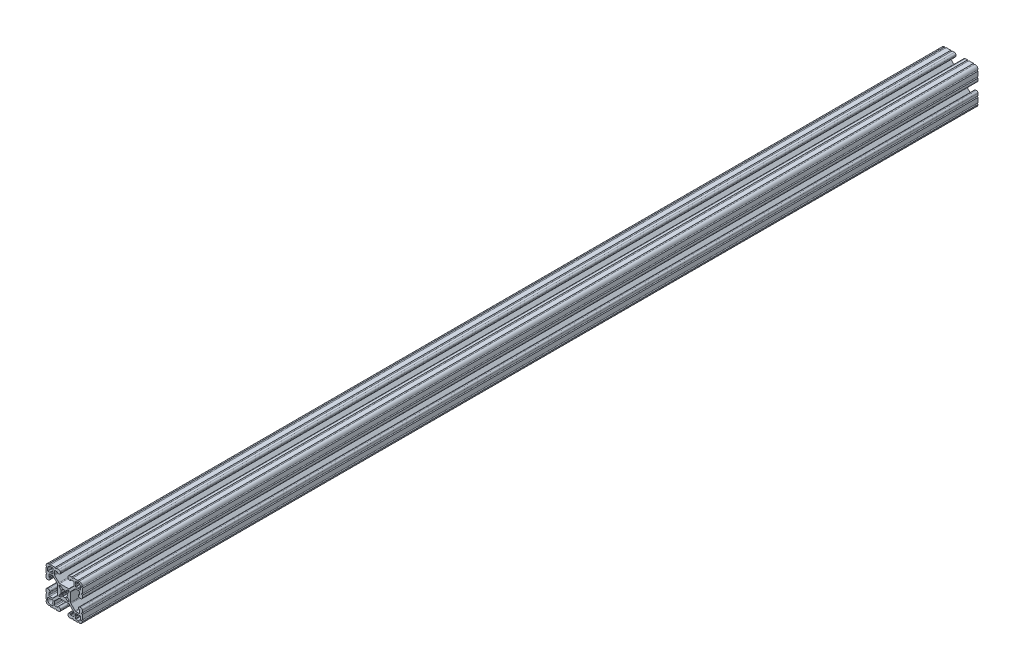
SolidWorks part; units mm, degrees
ref_plane "Front Plane" through (0, 0, 0) normal (0, 0, 1) x (1, 0, 0)
ref_plane "Top Plane" through (0, 0, 0) normal (0, 1, 0) x (1, 0, 0)
ref_plane "Right Plane" through (0, 0, 0) normal (1, 0, 0) x (0, 0, -1)
ref_plane "Plane1" through (0, 0, -2322.576) normal (0, 0, -1) x (-1, 0, 0)
sketch "Sketch1" plane through (0, 0, -2322.576) normal (0, 0, -1) x (-1, 0, 0)
  line L0 (17.2466, 14.4526) -> (17.2466, 12.2428)
  line L1 (16.8656, 11.8618) -> (15.0927, 11.8618)
  line L2 (15.0927, 11.8618) -> (14.5542, 12.4003)
  line L3 (14.5542, 12.4003) -> (14.0157, 11.8618)
  line L4 (14.0157, 11.8618) -> (12.2428, 11.8618)
  line L5 (11.8618, 12.2428) -> (11.8618, 14.0157)
  line L6 (11.8618, 14.0157) -> (12.4003, 14.5542)
  line L7 (12.4003, 14.5542) -> (11.8618, 15.0927)
  line L8 (11.8618, 15.0927) -> (11.8618, 16.8656)
  line L9 (12.2428, 17.2466) -> (14.4526, 17.2466)
  line L10 (17.2466, -12.2428) -> (17.2466, -14.4526)
  line L11 (14.4526, -17.2466) -> (12.2428, -17.2466)
  line L12 (11.8618, -16.8656) -> (11.8618, -15.0927)
  line L13 (11.8618, -15.0927) -> (12.4003, -14.5542)
  line L14 (12.4003, -14.5542) -> (11.8618, -14.0157)
  line L15 (11.8618, -14.0157) -> (11.8618, -12.2428)
  line L16 (12.2428, -11.8618) -> (14.0157, -11.8618)
  line L17 (14.0157, -11.8618) -> (14.5542, -12.4003)
  line L18 (14.5542, -12.4003) -> (15.0927, -11.8618)
  line L19 (15.0927, -11.8618) -> (16.8656, -11.8618)
  line L20 (5.1689, -3.9207) -> (5.1689, -4.9149)
  line L21 (4.9149, -5.1689) -> (3.9207, -5.1689)
  line L22 (3.2921, -4.9085) -> (1.5823, -3.1988)
  line L23 (-1.5823, -3.1988) -> (-3.2921, -4.9085)
  line L24 (-3.9207, -5.1689) -> (-4.9149, -5.1689)
  line L25 (-5.1689, -4.9149) -> (-5.1689, -3.9207)
  line L26 (-4.9085, -3.2921) -> (-3.1988, -1.5823)
  line L27 (-3.1988, 1.5823) -> (-4.9085, 3.2921)
  line L28 (-5.1689, 3.9207) -> (-5.1689, 4.9149)
  line L29 (-4.9149, 5.1689) -> (-3.9207, 5.1689)
  line L30 (-3.2921, 4.9085) -> (-1.5823, 3.1988)
  line L31 (1.5823, 3.1988) -> (3.2921, 4.9085)
  line L32 (3.9207, 5.1689) -> (4.9149, 5.1689)
  line L33 (5.1689, 4.9149) -> (5.1689, 3.9207)
  line L34 (4.9085, 3.2921) -> (3.1988, 1.5823)
  line L35 (3.1988, -1.5823) -> (4.9085, -3.2921)
  line L36 (-11.8618, -12.2428) -> (-11.8618, -14.0157)
  line L37 (-11.8618, -14.0157) -> (-12.4003, -14.5542)
  line L38 (-12.4003, -14.5542) -> (-11.8618, -15.0927)
  line L39 (-11.8618, -15.0927) -> (-11.8618, -16.8656)
  line L40 (-12.2428, -17.2466) -> (-14.4526, -17.2466)
  line L41 (-17.2466, -14.4526) -> (-17.2466, -12.2428)
  line L42 (-16.8656, -11.8618) -> (-15.0927, -11.8618)
  line L43 (-15.0927, -11.8618) -> (-14.5542, -12.4003)
  line L44 (-14.5542, -12.4003) -> (-14.0157, -11.8618)
  line L45 (-14.0157, -11.8618) -> (-12.2428, -11.8618)
  line L46 (-11.8618, 16.8656) -> (-11.8618, 15.0927)
  line L47 (-11.8618, 15.0927) -> (-12.4003, 14.5542)
  line L48 (-12.4003, 14.5542) -> (-11.8618, 14.0157)
  line L49 (-11.8618, 14.0157) -> (-11.8618, 12.2428)
  line L50 (-12.2428, 11.8618) -> (-14.0157, 11.8618)
  line L51 (-14.0157, 11.8618) -> (-14.5542, 12.4003)
  line L52 (-14.5542, 12.4003) -> (-15.0927, 11.8618)
  line L53 (-15.0927, 11.8618) -> (-16.8656, 11.8618)
  line L54 (-17.2466, 12.2428) -> (-17.2466, 14.4526)
  line L55 (-14.4526, 17.2466) -> (-12.2428, 17.2466)
  line L56 (19.05, -14.3256) -> (19.05, -9.4996)
  line L57 (19.05, -7.9756) -> (19.05, -5.6388)
  line L58 (17.4752, -4.064) -> (16.5608, -4.064)
  line L59 (14.986, -5.6388) -> (14.986, -6.35)
  line L60 (15.367, -6.731) -> (15.6972, -6.731)
  line L61 (16.0782, -7.112) -> (16.0782, -9.398)
  line L62 (15.1892, -10.287) -> (12.3756, -10.287)
  line L63 (11.4776, -9.915) -> (7.1157, -5.5531)
  line L64 (6.7437, -4.6551) -> (6.7437, 4.6551)
  line L65 (7.1157, 5.5531) -> (11.4776, 9.915)
  line L66 (12.3756, 10.287) -> (15.1892, 10.287)
  line L67 (16.0782, 9.398) -> (16.0782, 7.112)
  line L68 (15.6972, 6.731) -> (15.367, 6.731)
  line L69 (14.986, 6.35) -> (14.986, 5.6388)
  line L70 (16.5608, 4.064) -> (17.4752, 4.064)
  line L71 (19.05, 5.6388) -> (19.05, 7.9756)
  line L72 (19.05, 9.4996) -> (19.05, 14.3256)
  line L73 (14.3256, 19.05) -> (9.4996, 19.05)
  line L74 (7.9756, 19.05) -> (5.6388, 19.05)
  line L75 (4.064, 17.4752) -> (4.064, 16.5608)
  line L76 (5.6388, 14.986) -> (6.35, 14.986)
  line L77 (6.731, 15.367) -> (6.731, 15.6972)
  line L78 (7.112, 16.0782) -> (9.398, 16.0782)
  line L79 (10.287, 15.1892) -> (10.287, 12.3756)
  line L80 (9.915, 11.4776) -> (5.5531, 7.1157)
  line L81 (4.6551, 6.7437) -> (-4.6551, 6.7437)
  line L82 (-5.5531, 7.1157) -> (-9.915, 11.4776)
  line L83 (-10.287, 12.3756) -> (-10.287, 15.1892)
  line L84 (-9.398, 16.0782) -> (-7.112, 16.0782)
  line L85 (-6.731, 15.6972) -> (-6.731, 15.367)
  line L86 (-6.35, 14.986) -> (-5.6388, 14.986)
  line L87 (-4.064, 16.5608) -> (-4.064, 17.4752)
  line L88 (-5.6388, 19.05) -> (-7.9756, 19.05)
  line L89 (-9.4996, 19.05) -> (-14.3256, 19.05)
  line L90 (-19.05, 14.3256) -> (-19.05, 9.4996)
  line L91 (-19.05, 7.9756) -> (-19.05, 5.6388)
  line L92 (-17.4752, 4.064) -> (-16.5608, 4.064)
  line L93 (-14.986, 5.6388) -> (-14.986, 6.35)
  line L94 (-15.367, 6.731) -> (-15.6972, 6.731)
  line L95 (-16.0782, 7.112) -> (-16.0782, 9.398)
  line L96 (-15.1892, 10.287) -> (-12.3756, 10.287)
  line L97 (-11.4776, 9.915) -> (-7.1157, 5.5531)
  line L98 (-6.7437, 4.6551) -> (-6.7437, -4.6551)
  line L99 (-7.1157, -5.5531) -> (-11.4776, -9.915)
  line L100 (-12.3756, -10.287) -> (-15.1892, -10.287)
  line L101 (-16.0782, -9.398) -> (-16.0782, -7.112)
  line L102 (-15.6972, -6.731) -> (-15.367, -6.731)
  line L103 (-14.986, -6.35) -> (-14.986, -5.6388)
  line L104 (-16.5608, -4.064) -> (-17.4752, -4.064)
  line L105 (-19.05, -5.6388) -> (-19.05, -7.9756)
  line L106 (-19.05, -9.4996) -> (-19.05, -14.3256)
  line L107 (-14.3256, -19.05) -> (-9.4996, -19.05)
  line L108 (-7.9756, -19.05) -> (-5.6388, -19.05)
  line L109 (-4.064, -17.4752) -> (-4.064, -16.5608)
  line L110 (-5.6388, -14.986) -> (-6.35, -14.986)
  line L111 (-6.731, -15.367) -> (-6.731, -15.6972)
  line L112 (-7.112, -16.0782) -> (-9.398, -16.0782)
  line L113 (-10.287, -15.1892) -> (-10.287, -12.3756)
  line L114 (-9.915, -11.4776) -> (-5.5531, -7.1157)
  line L115 (-4.6551, -6.7437) -> (4.6551, -6.7437)
  line L116 (5.5531, -7.1157) -> (9.915, -11.4776)
  line L117 (10.287, -12.3756) -> (10.287, -15.1892)
  line L118 (9.398, -16.0782) -> (7.112, -16.0782)
  line L119 (6.731, -15.6972) -> (6.731, -15.367)
  line L120 (6.35, -14.986) -> (5.6388, -14.986)
  line L121 (4.064, -16.5608) -> (4.064, -17.4752)
  line L122 (5.6388, -19.05) -> (7.9756, -19.05)
  line L123 (9.4996, -19.05) -> (14.3256, -19.05)
  arc A0 (17.2466, 12.2428) -> (16.8656, 11.8618) centre (16.8656, 12.2428) cw
  arc A1 (12.2428, 11.8618) -> (11.8618, 12.2428) centre (12.2428, 12.2428) cw
  arc A2 (11.8618, 16.8656) -> (12.2428, 17.2466) centre (12.2428, 16.8656) cw
  arc A3 (14.4526, 17.2466) -> (17.2466, 14.4526) centre (14.4526, 14.4526) cw
  arc A4 (17.2466, -14.4526) -> (14.4526, -17.2466) centre (14.4526, -14.4526) cw
  arc A5 (12.2428, -17.2466) -> (11.8618, -16.8656) centre (12.2428, -16.8656) cw
  arc A6 (11.8618, -12.2428) -> (12.2428, -11.8618) centre (12.2428, -12.2428) cw
  arc A7 (16.8656, -11.8618) -> (17.2466, -12.2428) centre (16.8656, -12.2428) cw
  arc A8 (5.1689, -4.9149) -> (4.9149, -5.1689) centre (4.9149, -4.9149) cw
  arc A9 (3.9207, -5.1689) -> (3.2921, -4.9085) centre (3.9207, -4.2799) cw
  arc A10 (1.5823, -3.1988) -> (1.178, -3.1119) centre (1.3129, -3.4682) ccw
  arc A11 (1.178, -3.1119) -> (-1.178, -3.1119) centre (0, 0) cw
  arc A12 (-1.178, -3.1119) -> (-1.5823, -3.1988) centre (-1.3129, -3.4682) ccw
  arc A13 (-3.2921, -4.9085) -> (-3.9207, -5.1689) centre (-3.9207, -4.2799) cw
  arc A14 (-4.9149, -5.1689) -> (-5.1689, -4.9149) centre (-4.9149, -4.9149) cw
  arc A15 (-5.1689, -3.9207) -> (-4.9085, -3.2921) centre (-4.2799, -3.9207) cw
  arc A16 (-3.1988, -1.5823) -> (-3.1119, -1.178) centre (-3.4682, -1.3129) ccw
  arc A17 (-3.1119, -1.178) -> (-3.1119, 1.178) centre (0, 0) cw
  arc A18 (-3.1119, 1.178) -> (-3.1988, 1.5823) centre (-3.4682, 1.3129) ccw
  arc A19 (-4.9085, 3.2921) -> (-5.1689, 3.9207) centre (-4.2799, 3.9207) cw
  arc A20 (-5.1689, 4.9149) -> (-4.9149, 5.1689) centre (-4.9149, 4.9149) cw
  arc A21 (-3.9207, 5.1689) -> (-3.2921, 4.9085) centre (-3.9207, 4.2799) cw
  arc A22 (-1.5823, 3.1988) -> (-1.178, 3.1119) centre (-1.3129, 3.4682) ccw
  arc A23 (-1.178, 3.1119) -> (1.178, 3.1119) centre (0, 0) cw
  arc A24 (1.178, 3.1119) -> (1.5823, 3.1988) centre (1.3129, 3.4682) ccw
  arc A25 (3.2921, 4.9085) -> (3.9207, 5.1689) centre (3.9207, 4.2799) cw
  arc A26 (4.9149, 5.1689) -> (5.1689, 4.9149) centre (4.9149, 4.9149) cw
  arc A27 (5.1689, 3.9207) -> (4.9085, 3.2921) centre (4.2799, 3.9207) cw
  arc A28 (3.1988, 1.5823) -> (3.1119, 1.178) centre (3.4682, 1.3129) ccw
  arc A29 (3.1119, 1.178) -> (3.1119, -1.178) centre (0, 0) cw
  arc A30 (3.1119, -1.178) -> (3.1988, -1.5823) centre (3.4682, -1.3129) ccw
  arc A31 (4.9085, -3.2921) -> (5.1689, -3.9207) centre (4.2799, -3.9207) cw
  arc A32 (-11.8618, -16.8656) -> (-12.2428, -17.2466) centre (-12.2428, -16.8656) cw
  arc A33 (-14.4526, -17.2466) -> (-17.2466, -14.4526) centre (-14.4526, -14.4526) cw
  arc A34 (-17.2466, -12.2428) -> (-16.8656, -11.8618) centre (-16.8656, -12.2428) cw
  arc A35 (-12.2428, -11.8618) -> (-11.8618, -12.2428) centre (-12.2428, -12.2428) cw
  arc A36 (-12.2428, 17.2466) -> (-11.8618, 16.8656) centre (-12.2428, 16.8656) cw
  arc A37 (-11.8618, 12.2428) -> (-12.2428, 11.8618) centre (-12.2428, 12.2428) cw
  arc A38 (-16.8656, 11.8618) -> (-17.2466, 12.2428) centre (-16.8656, 12.2428) cw
  arc A39 (-17.2466, 14.4526) -> (-14.4526, 17.2466) centre (-14.4526, 14.4526) cw
  arc A40 (19.05, -9.4996) -> (19.05, -7.9756) centre (19.05, -8.7376) cw
  arc A41 (19.05, -5.6388) -> (17.4752, -4.064) centre (17.4752, -5.6388) ccw
  arc A42 (16.5608, -4.064) -> (14.986, -5.6388) centre (16.5608, -5.6388) ccw
  arc A43 (14.986, -6.35) -> (15.367, -6.731) centre (15.367, -6.35) ccw
  arc A44 (15.6972, -6.731) -> (16.0782, -7.112) centre (15.6972, -7.112) cw
  arc A45 (16.0782, -9.398) -> (15.1892, -10.287) centre (15.1892, -9.398) cw
  arc A46 (12.3756, -10.287) -> (11.4776, -9.915) centre (12.3756, -9.017) cw
  arc A47 (7.1157, -5.5531) -> (6.7437, -4.6551) centre (8.0137, -4.6551) cw
  arc A48 (6.7437, 4.6551) -> (7.1157, 5.5531) centre (8.0137, 4.6551) cw
  arc A49 (11.4776, 9.915) -> (12.3756, 10.287) centre (12.3756, 9.017) cw
  arc A50 (15.1892, 10.287) -> (16.0782, 9.398) centre (15.1892, 9.398) cw
  arc A51 (16.0782, 7.112) -> (15.6972, 6.731) centre (15.6972, 7.112) cw
  arc A52 (15.367, 6.731) -> (14.986, 6.35) centre (15.367, 6.35) ccw
  arc A53 (14.986, 5.6388) -> (16.5608, 4.064) centre (16.5608, 5.6388) ccw
  arc A54 (17.4752, 4.064) -> (19.05, 5.6388) centre (17.4752, 5.6388) ccw
  arc A55 (19.05, 7.9756) -> (19.05, 9.4996) centre (19.05, 8.7376) cw
  arc A56 (19.05, 14.3256) -> (19.0499, 15.8496) centre (19.05, 15.0876) cw
  arc A57 (19.0499, 15.8496) -> (15.8496, 19.0499) centre (15.875, 15.875) ccw
  arc A58 (15.8496, 19.0499) -> (14.3256, 19.05) centre (15.0876, 19.05) cw
  arc A59 (9.4996, 19.05) -> (7.9756, 19.05) centre (8.7376, 19.05) cw
  arc A60 (5.6388, 19.05) -> (4.064, 17.4752) centre (5.6388, 17.4752) ccw
  arc A61 (4.064, 16.5608) -> (5.6388, 14.986) centre (5.6388, 16.5608) ccw
  arc A62 (6.35, 14.986) -> (6.731, 15.367) centre (6.35, 15.367) ccw
  arc A63 (6.731, 15.6972) -> (7.112, 16.0782) centre (7.112, 15.6972) cw
  arc A64 (9.398, 16.0782) -> (10.287, 15.1892) centre (9.398, 15.1892) cw
  arc A65 (10.287, 12.3756) -> (9.915, 11.4776) centre (9.017, 12.3756) cw
  arc A66 (5.5531, 7.1157) -> (4.6551, 6.7437) centre (4.6551, 8.0137) cw
  arc A67 (-4.6551, 6.7437) -> (-5.5531, 7.1157) centre (-4.6551, 8.0137) cw
  arc A68 (-9.915, 11.4776) -> (-10.287, 12.3756) centre (-9.017, 12.3756) cw
  arc A69 (-10.287, 15.1892) -> (-9.398, 16.0782) centre (-9.398, 15.1892) cw
  arc A70 (-7.112, 16.0782) -> (-6.731, 15.6972) centre (-7.112, 15.6972) cw
  arc A71 (-6.731, 15.367) -> (-6.35, 14.986) centre (-6.35, 15.367) ccw
  arc A72 (-5.6388, 14.986) -> (-4.064, 16.5608) centre (-5.6388, 16.5608) ccw
  arc A73 (-4.064, 17.4752) -> (-5.6388, 19.05) centre (-5.6388, 17.4752) ccw
  arc A74 (-7.9756, 19.05) -> (-9.4996, 19.05) centre (-8.7376, 19.05) cw
  arc A75 (-14.3256, 19.05) -> (-15.8496, 19.0499) centre (-15.0876, 19.05) cw
  arc A76 (-15.8496, 19.0499) -> (-19.0499, 15.8496) centre (-15.875, 15.875) ccw
  arc A77 (-19.0499, 15.8496) -> (-19.05, 14.3256) centre (-19.05, 15.0876) cw
  arc A78 (-19.05, 9.4996) -> (-19.05, 7.9756) centre (-19.05, 8.7376) cw
  arc A79 (-19.05, 5.6388) -> (-17.4752, 4.064) centre (-17.4752, 5.6388) ccw
  arc A80 (-16.5608, 4.064) -> (-14.986, 5.6388) centre (-16.5608, 5.6388) ccw
  arc A81 (-14.986, 6.35) -> (-15.367, 6.731) centre (-15.367, 6.35) ccw
  arc A82 (-15.6972, 6.731) -> (-16.0782, 7.112) centre (-15.6972, 7.112) cw
  arc A83 (-16.0782, 9.398) -> (-15.1892, 10.287) centre (-15.1892, 9.398) cw
  arc A84 (-12.3756, 10.287) -> (-11.4776, 9.915) centre (-12.3756, 9.017) cw
  arc A85 (-7.1157, 5.5531) -> (-6.7437, 4.6551) centre (-8.0137, 4.6551) cw
  arc A86 (-6.7437, -4.6551) -> (-7.1157, -5.5531) centre (-8.0137, -4.6551) cw
  arc A87 (-11.4776, -9.915) -> (-12.3756, -10.287) centre (-12.3756, -9.017) cw
  arc A88 (-15.1892, -10.287) -> (-16.0782, -9.398) centre (-15.1892, -9.398) cw
  arc A89 (-16.0782, -7.112) -> (-15.6972, -6.731) centre (-15.6972, -7.112) cw
  arc A90 (-15.367, -6.731) -> (-14.986, -6.35) centre (-15.367, -6.35) ccw
  arc A91 (-14.986, -5.6388) -> (-16.5608, -4.064) centre (-16.5608, -5.6388) ccw
  arc A92 (-17.4752, -4.064) -> (-19.05, -5.6388) centre (-17.4752, -5.6388) ccw
  arc A93 (-19.05, -7.9756) -> (-19.05, -9.4996) centre (-19.05, -8.7376) cw
  arc A94 (-19.05, -14.3256) -> (-19.0499, -15.8496) centre (-19.05, -15.0876) cw
  arc A95 (-19.0499, -15.8496) -> (-15.8496, -19.0499) centre (-15.875, -15.875) ccw
  arc A96 (-15.8496, -19.0499) -> (-14.3256, -19.05) centre (-15.0876, -19.05) cw
  arc A97 (-9.4996, -19.05) -> (-7.9756, -19.05) centre (-8.7376, -19.05) cw
  arc A98 (-5.6388, -19.05) -> (-4.064, -17.4752) centre (-5.6388, -17.4752) ccw
  arc A99 (-4.064, -16.5608) -> (-5.6388, -14.986) centre (-5.6388, -16.5608) ccw
  arc A100 (-6.35, -14.986) -> (-6.731, -15.367) centre (-6.35, -15.367) ccw
  arc A101 (-6.731, -15.6972) -> (-7.112, -16.0782) centre (-7.112, -15.6972) cw
  arc A102 (-9.398, -16.0782) -> (-10.287, -15.1892) centre (-9.398, -15.1892) cw
  arc A103 (-10.287, -12.3756) -> (-9.915, -11.4776) centre (-9.017, -12.3756) cw
  arc A104 (-5.5531, -7.1157) -> (-4.6551, -6.7437) centre (-4.6551, -8.0137) cw
  arc A105 (4.6551, -6.7437) -> (5.5531, -7.1157) centre (4.6551, -8.0137) cw
  arc A106 (9.915, -11.4776) -> (10.287, -12.3756) centre (9.017, -12.3756) cw
  arc A107 (10.287, -15.1892) -> (9.398, -16.0782) centre (9.398, -15.1892) cw
  arc A108 (7.112, -16.0782) -> (6.731, -15.6972) centre (7.112, -15.6972) cw
  arc A109 (6.731, -15.367) -> (6.35, -14.986) centre (6.35, -15.367) ccw
  arc A110 (5.6388, -14.986) -> (4.064, -16.5608) centre (5.6388, -16.5608) ccw
  arc A111 (4.064, -17.4752) -> (5.6388, -19.05) centre (5.6388, -17.4752) ccw
  arc A112 (7.9756, -19.05) -> (9.4996, -19.05) centre (8.7376, -19.05) cw
  arc A113 (14.3256, -19.05) -> (15.8496, -19.0499) centre (15.0876, -19.05) cw
  arc A114 (15.8496, -19.0499) -> (19.0499, -15.8496) centre (15.875, -15.875) ccw
  arc A115 (19.0499, -15.8496) -> (19.05, -14.3256) centre (19.05, -15.0876) cw
extrude "Boss-Extrude1" add sketch "Sketch1" against normal blind 939.8
